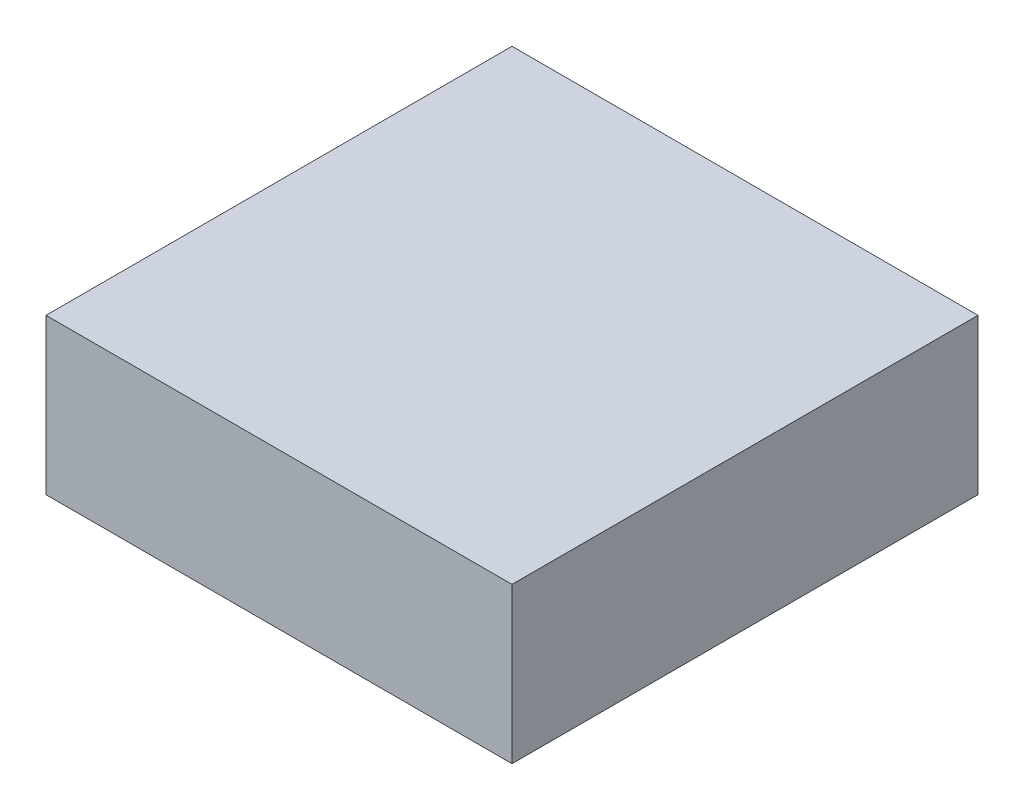
SolidWorks part; units mm, degrees
ref_plane "Front Plane" through (0, 0, 0) normal (0, 0, 1) x (1, 0, 0)
ref_plane "Top Plane" through (0, 0, 0) normal (0, 1, 0) x (1, 0, 0)
ref_plane "Right Plane" through (0, 0, 0) normal (1, 0, 0) x (0, 0, -1)
sketch "Sketch1" plane through (0, 0, 0) normal (0, 1, 0) x (1, 0, 0)
  line L1 (-89.3348, -52.4179) -> (0.6652, -52.4179)
  line L2 (-89.3348, -52.4179) -> (-89.3348, 37.5821)
  line L3 (-89.3348, 37.5821) -> (0.6652, 37.5821)
  line L4 (0.6652, -52.4179) -> (0.6652, 37.5821)
extrude "Boss-Extrude1" add sketch "Sketch1" against normal blind 30
